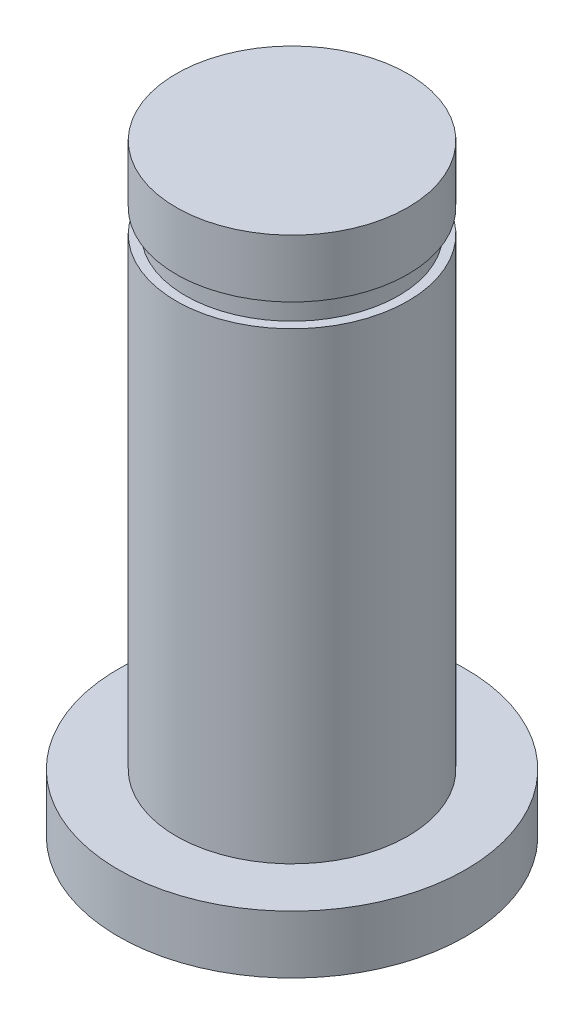
SolidWorks part; units mm, degrees
material "AISI 316 Annealed Stainless Steel Bar (SS)"
ref_plane "Front Plane" through (0, 0, 0) normal (0, 0, 1) x (1, 0, 0)
ref_plane "Top Plane" through (0, 0, 0) normal (0, 1, 0) x (1, 0, 0)
ref_plane "Right Plane" through (0, 0, 0) normal (1, 0, 0) x (0, 0, -1)
sketch "Sketch1" plane through (0, 0, 0) normal (0, 0, 1) x (1, 0, 0)
  line L0 (0, 0) -> (-3.175, 0)
  line L1 (-3.175, 0) -> (-3.175, -1.5875)
  line L2 (-3.175, -1.5875) -> (-2.921, -1.5875)
  line L3 (-2.921, -1.5875) -> (-2.921, -2.2225)
  line L4 (-2.921, -2.2225) -> (-3.175, -2.2225)
  line L5 (-3.175, -2.2225) -> (-3.175, -14.9225)
  line L9 (-4.7625, -14.9225) -> (-4.7625, -16.51)
  line L10 (-4.7625, -16.51) -> (0, -16.51)
  line L11 (0, -16.51) -> (0, 0)
  line L12 (-4.7625, -14.9225) -> (-3.175, -14.9225)
  dimension "D1" = 3.175
  dimension "D2" = 4.7625
  dimension "D3" = 3.175
  dimension "D4" = 0.254
  dimension "D5" = 0.635
  dimension "D6" = 12.7
  dimension "D7" = 1.5875
  dimension "D8" = 1.5875
revolve "Revolve1" add sketch "Sketch1" angle 360 about L11
